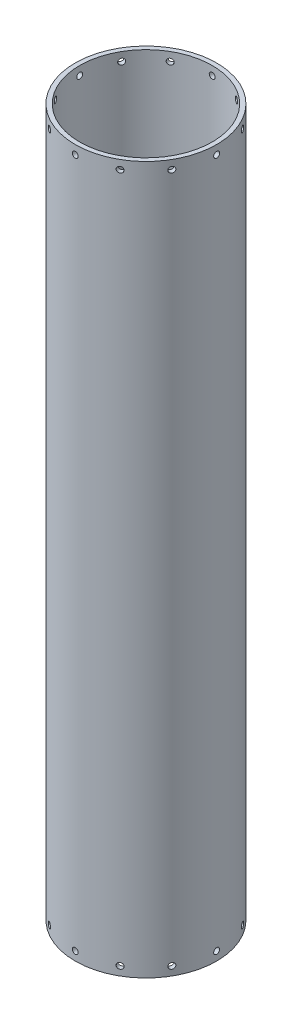
SolidWorks part; units mm, degrees
material "6061-T6 (SS)"
ref_plane "Front Plane" through (0, 0, 0) normal (0, 0, 1) x (1, 0, 0)
ref_plane "Top Plane" through (0, 0, 0) normal (0, 1, 0) x (1, 0, 0)
ref_plane "Right Plane" through (0, 0, 0) normal (1, 0, 0) x (0, 0, -1)
sketch "Sketch1" plane through (0, 0, 0) normal (0, 1, 0) x (1, 0, 0)
  circle A0 centre (0, 0) radius 76.2
  circle A1 centre (0, 0) radius 71.4375
  dimension "D1" = 152.4
  dimension "D2" = 142.875
extrude "Inner&OuterDiameter" add sketch "Sketch1" along normal blind 762
sketch "Sketch2" plane through (0, 0, 0) normal (0, 0, 1) x (1, 0, 0)
  line L0 (71.4375, 762) -> (-71.4375, 762) construction
  line L1 (-76.2, 0) -> (76.2, 0) construction
  circle A0 centre (0, 752.475) radius 3.175
  circle A1 centre (0, 9.525) radius 3.175
  dimension "D2" = 6.35
  dimension "D3" = 6.35
  dimension "D1" = 9.525
  dimension "D4" = 9.525
extrude "Top&BottomBoltHoles" cut sketch "Sketch2" against normal through all
pattern_circular "CirPattern1" count 12 over 360 about axis through (0, 762, 0) along (0, -1, 0) of "Top&BottomBoltHoles"
